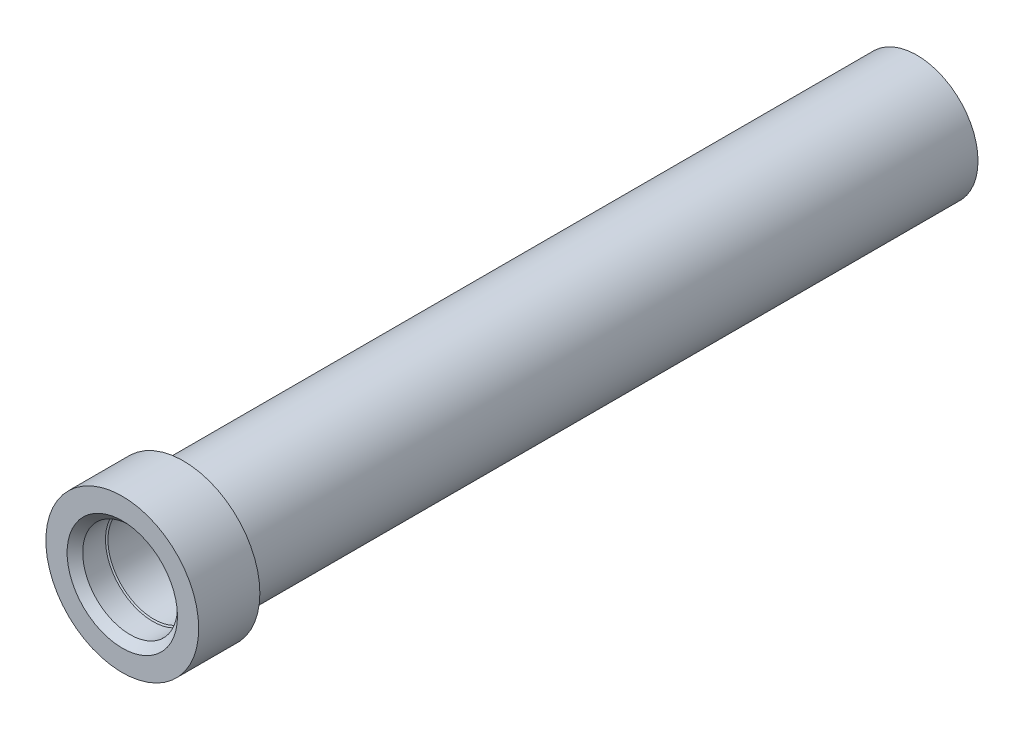
SolidWorks part; units mm, degrees
ref_plane "Front Plane" through (0, 0, 0) normal (0, 0, 1) x (1, 0, 0)
ref_plane "Top Plane" through (0, 0, 0) normal (0, 1, 0) x (1, 0, 0)
ref_plane "Right Plane" through (0, 0, 0) normal (1, 0, 0) x (0, 0, -1)
sketch "Sketch3" plane through (0, 0, 0) normal (1, 0, 0) x (0, 0, -1)
  line L2 (0, 12.5) -> (10, 12.5)
  line L3 (10, 12.5) -> (10, 10)
  line L4 (10, 10) -> (129.95, 10)
  line L5 (129.95, 10) -> (129.95, 0)
  line L11 (0, 12.5) -> (0, 0)
  line L12 (0, 0) -> (129.95, 0)
  dimension "D1" = 12.5
  dimension "Altura" = 129.95
  dimension "D2" = 10
  dimension "Altura_Base" = 10
revolve "Revolve2" add sketch "Sketch3" angle 360 about L12
sketch "Sketch4" plane through (0, 0, -129.95) normal (0, 0, -1) x (-1, 0, 0)
  circle A0 centre (0, 0) radius 5
  dimension "D1" = 10
extrude "Cut-Extrude1" cut sketch "Sketch4" against normal up to surface (119.95 mm away) up to face at (12.5, 0, -10)
sketch "Sketch5" plane through (0, 0, 0) normal (0, 0, 1) x (1, 0, 0)
  circle A0 centre (0, 0) radius 7.5
  dimension "D1" = 15
extrude "Cut-Extrude2" cut sketch "Sketch5" against normal blind 80
sketch "Sketch8" [suppressed] plane through (0, 0, 0) normal (0, 0, 1) x (1, 0, 0)
  circle A0 centre (0, 0) radius 7.5
  dimension "D1" = 15
extrude "Boss-Extrude1" [suppressed] add sketch "Sketch8" along normal blind 17.5
other "M12 Machine Threads Stud1" [suppressed] parameters "D1"=12, "D2"=10, "D3"=17.5, "D4"=15
sketch "Sketch9" plane through (0, 0, 17.5) normal (1, 0, 0) x (0, 1, 0)
  line L5 (0, -14.3089) -> (0, 0) construction
  line L6 (5.036, 0) -> (6, -0.964)
  line L9 (6, -0.964) -> (6, -17.5)
  line L10 (5.036, 0) -> (7.5, 0)
  line L11 (7.5, 0) -> (7.5, -17.5)
  line L12 (6, -17.5) -> (7.5, -17.5)
  dimension "Minor Diameter" = 10.072
  dimension "Major Diameter" = 12
  dimension "Thread Length" = 17.5
  dimension "Cylinder Diameter" = 15
  dimension "Chamfer Angle" = 45
cosmetic thread "Stud Thread2" [suppressed] parameters "D2"=10.072
hole_wizard "M18 Tapped Hole1" positions "Sketch12" profile "Sketch13" tap size "M18" standard "ISO"
sketch "Sketch12" plane through (0, 0, 0) normal (0, 0, 1) x (1, 0, 0)
  point P0 (0, 0)
sketch "Sketch13" plane through (0, 0, 0) normal (1, 0, 0) x (0, -1, 0)
  line L0 (0, 0) -> (0, 9.6567)
  line L1 (0, 9.6567) -> (7.75, 5)
  line L2 (7.75, 5) -> (7.75, 1.275)
  line L3 (7.75, 1.275) -> (9.025, 0)
  line L5 (9.025, 0) -> (0, 0)
  line L6 (-7.75, 1.275) -> (-9.025, 0) construction
  line L10 (0, 9.6567) -> (-7.75, 5) construction
  line L11 (0, -6.35) -> (0, 107.95) construction
  dimension "Tap Drill Dia." = 15.5
  dimension "Tap Drill Depth" = 5
  dimension "Near C'Sink Dia." = 18.05
  dimension "Near C'Sink Angle" = 90
  dimension "Drill Angle" = 118
cosmetic thread "Hole Thread1" parameters "D1"=5, "D2"=18
equation "\"Altura\"=30"
